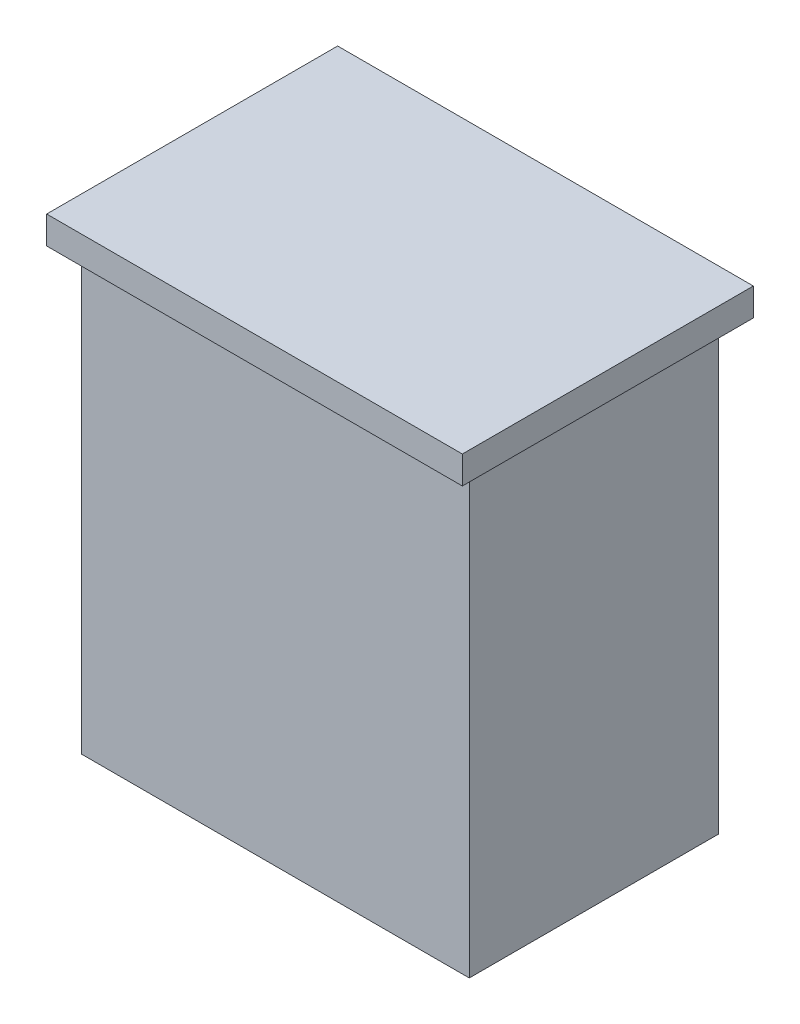
SolidWorks part; units mm, degrees
ref_plane "前视基准面" through (0, 0, 0) normal (0, 0, 1) x (1, 0, 0)
ref_plane "上视基准面" through (0, 0, 0) normal (0, 1, 0) x (1, 0, 0)
ref_plane "右视基准面" through (0, 0, 0) normal (1, 0, 0) x (0, 0, -1)
sketch "草图1" plane through (0, 0, 0) normal (0, 1, 0) x (1, 0, 0)
  line L1 (-7, 4.5) -> (7, 4.5)
  line L2 (-7, 4.5) -> (-7, -4.5)
  line L3 (-7, -4.5) -> (7, -4.5)
  line L4 (7, 4.5) -> (7, -4.5)
  line L5 (-7, 4.5) -> (7, -4.5) construction
  line L6 (-7, -4.5) -> (7, 4.5) construction
  point P0 (0, 0)
  dimension "D1" = 14
  dimension "D2" = 9
extrude "凸台-拉伸1" add sketch "草图1" along normal blind 16
sketch "草图2" plane through (0, 16, 0) normal (0, 1, 0) x (1, 0, 0)
  line L1 (-7.5, 5.25) -> (7.5, 5.25)
  line L2 (-7.5, 5.25) -> (-7.5, -5.25)
  line L3 (-7.5, -5.25) -> (7.5, -5.25)
  line L4 (7.5, 5.25) -> (7.5, -5.25)
  line L5 (-7.5, 5.25) -> (7.5, -5.25) construction
  line L6 (-7.5, -5.25) -> (7.5, 5.25) construction
  point P0 (0, 0)
  dimension "D1" = 15
  dimension "D2" = 10.5
extrude "凸台-拉伸2" add sketch "草图2" along normal blind 1
